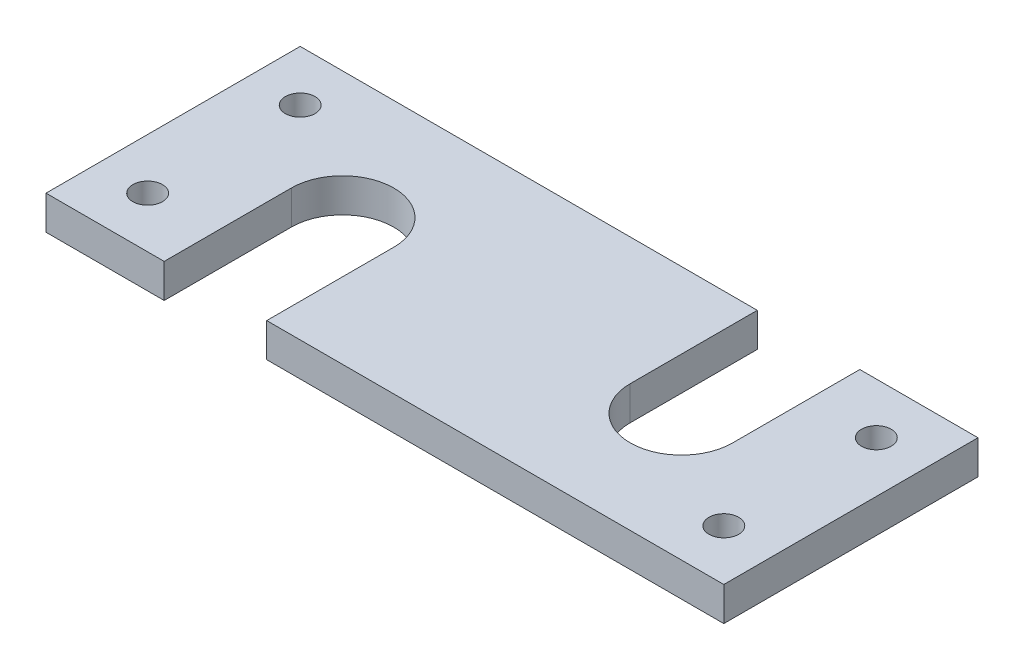
SolidWorks part; units mm, degrees
material "Balsa"
ref_plane "Front Plane" through (0, 0, 0) normal (0, 0, 1) x (1, 0, 0)
ref_plane "Top Plane" through (0, 0, 0) normal (0, 1, 0) x (1, 0, 0)
ref_plane "Right Plane" through (0, 0, 0) normal (1, 0, 0) x (0, 0, -1)
sketch "Sketch2" plane through (0, 0, 0) normal (0, 1, 0) x (1, 0, 0)
  line L0 (0, 0) -> (0, 30)
  line L1 (0, 0) -> (80, 0)
  line L2 (0, 30) -> (80, 30)
  line L3 (80, 0) -> (80, 30)
  dimension "D1" = 30
  dimension "D2" = 80
extrude "Boss-Extrude1" add sketch "Sketch2" along normal blind 4
sketch "Sketch3" plane through (0, 4, 0) normal (0, 1, 0) x (1, 0, 0)
  line L0 (13.95, 0) -> (26.05, 0)
  line L1 (0, 0) -> (80, 0) construction
  line L2 (26.05, 0) -> (26.05, 15)
  line L3 (0, 30) -> (0, 0) construction
  line L4 (13.95, 15) -> (13.95, 0)
  line L5 (53.95, 30) -> (53.95, 15)
  line L6 (80, 30) -> (0, 30) construction
  line L7 (80, 0) -> (80, 30) construction
  line L8 (66.05, 15) -> (66.05, 30)
  line L9 (66.05, 30) -> (53.95, 30)
  arc A0 (13.95, 15) -> (26.05, 15) centre (20, 15) cw
  arc A1 (53.95, 15) -> (66.05, 15) centre (60, 15) ccw
  circle A2 centre (6, 6) radius 1.75
  circle A3 centre (6, 24) radius 1.75
  circle A4 centre (74, 24) radius 1.75
  circle A5 centre (74, 6) radius 1.75
  dimension "D1" = 12.1
  dimension "D5" = 3.5
  dimension "D7" = 6
  dimension "D8" = 6
  dimension "D9" = 6
  dimension "D2" = 20
  dimension "D3" = 40
  dimension "D4" = 15
  dimension "D6" = 6
extrude "Cut-Extrude1" cut sketch "Sketch3" against normal through all
